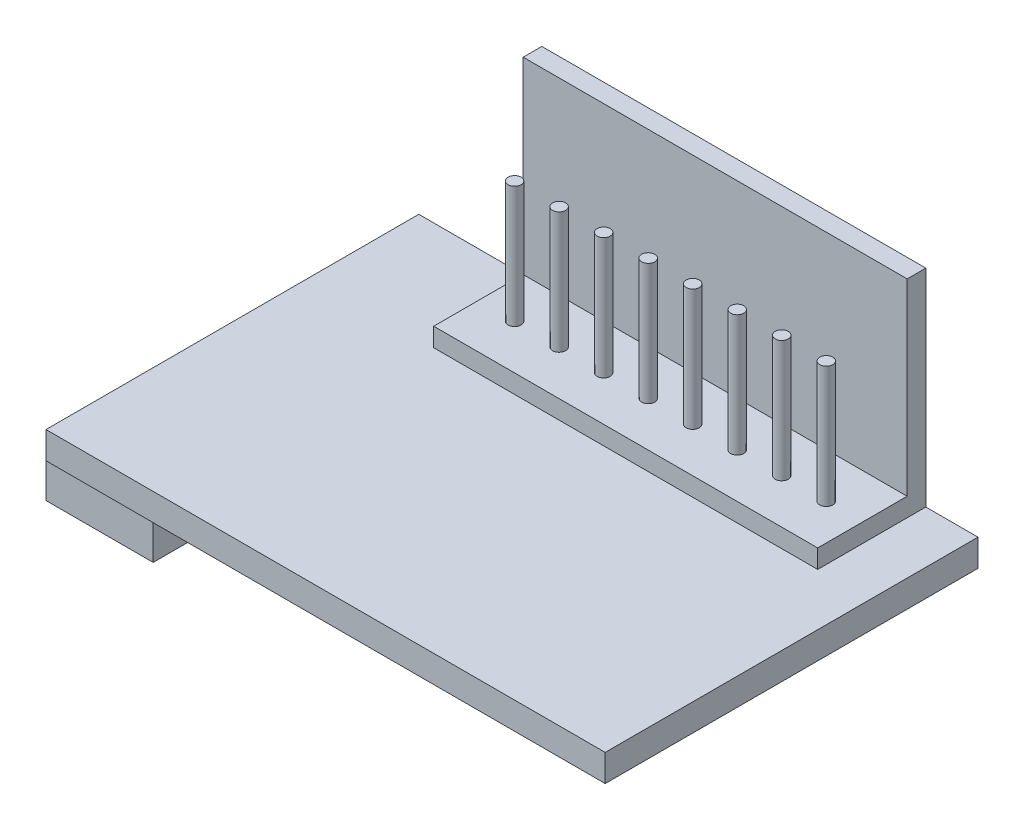
SolidWorks part; units mm, degrees
ref_plane "Front" through (0, 0, 0) normal (0, 0, 1) x (1, 0, 0)
ref_plane "Top" through (0, 0, 0) normal (0, 1, 0) x (1, 0, 0)
ref_plane "Right" through (0, 0, 0) normal (1, 0, 0) x (0, 0, -1)
sketch "Sketch1" plane through (0, 0, 0) normal (0, 1, 0) x (1, 0, 0)
  line L1 (0, 0) -> (30, 0)
  line L2 (0, 0) -> (0, 20)
  line L3 (0, 20) -> (30, 20)
  line L4 (30, 0) -> (30, 20)
  dimension "D1" = 30
  dimension "D2" = 20
extrude "Boss-Extrude1" add sketch "Sketch1" along normal blind 1.45
sketch "Sketch2" plane through (0, 1.45, 0) normal (0, 1, 0) x (1, 0, 0)
  line L0 (30, 20) -> (0, 20) construction
  line L1 (6.6, 20) -> (27.2, 20)
  line L2 (6.6, 20) -> (6.6, 14.2)
  line L3 (6.6, 14.2) -> (27.2, 14.2)
  line L4 (27.2, 20) -> (27.2, 14.2)
  line L6 (0, 20) -> (0, 0) construction
  dimension "D1" = 6.6
  dimension "D2" = 20.6
  dimension "D3" = 5.8
extrude "Boss-Extrude2" add sketch "Sketch2" along normal blind 11.1 separate body
sketch "Sketch4" plane through (0, 0, 0) normal (0, -1, 0) x (1, 0, 0)
  line L1 (-1, -1) -> (4.75, -1)
  line L2 (-1, -1) -> (-1, -16.5)
  line L3 (-1, -16.5) -> (4.75, -16.5)
  line L4 (4.75, -1) -> (4.75, -16.5)
  line L5 (0, -20) -> (0, 0) construction
  line L6 (0, 0) -> (30, 0) construction
  dimension "D1" = 1
  dimension "D2" = 15.5
  dimension "D3" = 5.75
  dimension "D4" = 1
extrude "Boss-Extrude3" add sketch "Sketch4" along normal blind 2.85 separate body
sketch "Sketch5" plane through (0, 0, -14.2) normal (0, 0, 1) x (1, 0, 0)
  line L0 (27.2, 12.55) -> (27.2, 1.45) construction
  line L1 (6.6, 12.55) -> (27.2, 12.55)
  line L2 (6.6, 12.55) -> (6.6, 2.45)
  line L3 (6.6, 2.45) -> (27.2, 2.45)
  line L4 (27.2, 12.55) -> (27.2, 2.45)
  line L6 (0, 1.45) -> (30, 1.45) construction
  dimension "D1" = 1
extrude "Cut-Extrude1" cut sketch "Sketch5" against normal offset from surface (4.8 mm away) 1 up to face at (16.9, 7, -20)
sketch "Sketch6" plane through (0, 2.45, 0) normal (0, 1, 0) x (1, 0, 0)
  line L0 (6.6, 16.6) -> (27.2, 16.6) construction
  line L1 (6.6, 19) -> (6.6, 14.2) construction
  line L2 (27.2, 19) -> (27.2, 14.2) construction
  line L3 (16.9, 19) -> (16.9, 14.2) construction
  line L4 (27.2, 19) -> (6.6, 19) construction
  line L5 (6.6, 14.2) -> (27.2, 14.2) construction
  circle A0 centre (8.5394, 16.6) radius 0.35
  circle A1 centre (10.9282, 16.6) radius 0.35
  circle A2 centre (13.3169, 16.6) radius 0.35
  circle A3 centre (15.7056, 16.6) radius 0.35
  circle A4 centre (18.0944, 16.6) radius 0.35
  circle A5 centre (20.4831, 16.6) radius 0.35
  circle A6 centre (22.8718, 16.6) radius 0.35
  circle A7 centre (25.2606, 16.6) radius 0.35
  dimension "D1" = 0.7
  dimension "D2" = 8
extrude "Boss-Extrude4" add sketch "Sketch6" along normal blind 6.52 separate body
